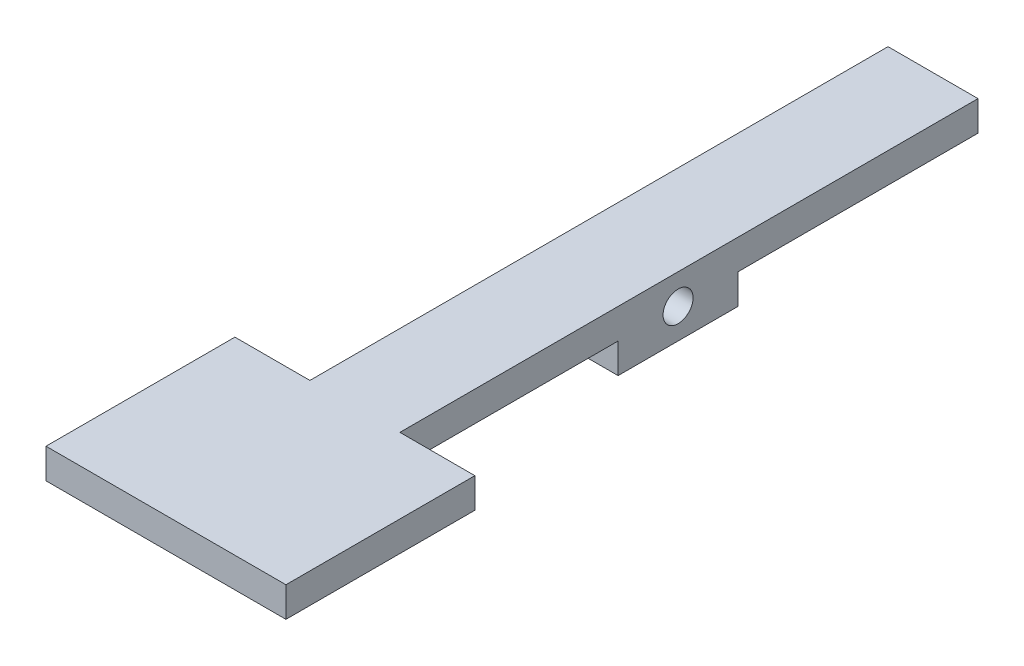
SolidWorks part; units mm, degrees
material "6061 Alloy"
ref_plane "Front Plane" through (0, 0, 0) normal (0, 0, 1) x (1, 0, 0)
ref_plane "Top Plane" through (0, 0, 0) normal (0, 1, 0) x (1, 0, 0)
ref_plane "Right Plane" through (0, 0, 0) normal (1, 0, 0) x (0, 0, -1)
sketch "Sketch1" plane through (0, 0, 0) normal (1, 0, 0) x (0, 0, -1)
  line L0 (0, 1.5875) -> (0, -1.5875)
  line L1 (0, -1.5875) -> (-25.4, -1.5875)
  line L5 (-76.2, 1.5875) -> (0, 1.5875)
  line L6 (-38.1, -1.5875) -> (-76.2, -1.5875)
  line L8 (-38.1, -1.5875) -> (-38.1, -4.7625)
  line L9 (-38.1, -4.7625) -> (-25.4, -4.7625)
  line L10 (-25.4, -1.5875) -> (-25.4, -4.7625)
  line L11 (-76.2, 1.5875) -> (-76.2, -1.5875)
  circle A0 centre (-31.75, -1.5875) radius 1.5875
  point P14 (-31.75, -4.7625)
  dimension "D6" = 3.175
  dimension "D1" = 3.175
  dimension "D4" = 76.2
  dimension "D5" = 3.175
  dimension "D7" = 12.7
  dimension "D8" = 38.1
extrude "Boss-Extrude1" add sketch "Sketch1" along normal blind 9.525
ref_plane "Center Plane" through (4.7625, 0, 0) normal (1, 0, 0) x (0, 0, -1)
sketch "Sketch3" plane through (4.7625, 0, 0) normal (1, 0, 0) x (0, 0, -1)
  line L2 (-76.2, -1.5875) -> (-61.2, -1.5875)
  line L4 (-61.2, -1.5875) -> (-61.2, 1.5875)
  line L5 (-76.2, 1.5875) -> (0, 1.5875) construction
  line L6 (-61.2, 1.5875) -> (-76.2, 1.5875)
  line L7 (-76.2, 1.5875) -> (-76.2, -1.5875)
  line L9 (-76.2, 1.5875) -> (-81.2, 1.5875)
  line L10 (-76.2, 1.5875) -> (-76.2, -1.5875)
  line L11 (-76.2, -1.5875) -> (-81.2, -1.5875)
  line L12 (-81.2, 1.5875) -> (-81.2, -1.5875)
  line L13 (-76.2, 1.5875) -> (-76.2, -1.5875) construction
  line L14 (-38.1, -1.5875) -> (-76.2, -1.5875) construction
  dimension "D1" = 15
  dimension "D2" = 20
extrude "Boss-Extrude2" add sketch "Sketch3" along normal mid plane 25.4 contours L6 L7 L2 L4 | L9 L12 L11 L7
fillet "Fillet1" [suppressed] radius 6.35
sketch "Sketch4" plane through (9.525, 0, 0) normal (1, 0, 0) x (0, 0, -1)
  line L0 (-38.1, -4.7625) -> (-25.4, -4.7625) construction
  line L1 (-25.4, -1.5875) -> (0, -1.5875)
  line L2 (-25.4, -1.5875) -> (-25.4, -4.7625)
  line L3 (-25.4, -4.7625) -> (0, -4.7625)
  line L4 (0, -1.5875) -> (0, -4.7625)
extrude "Boss-Extrude3" [suppressed] add sketch "Sketch4" against normal up to surface (9.525 mm away)
